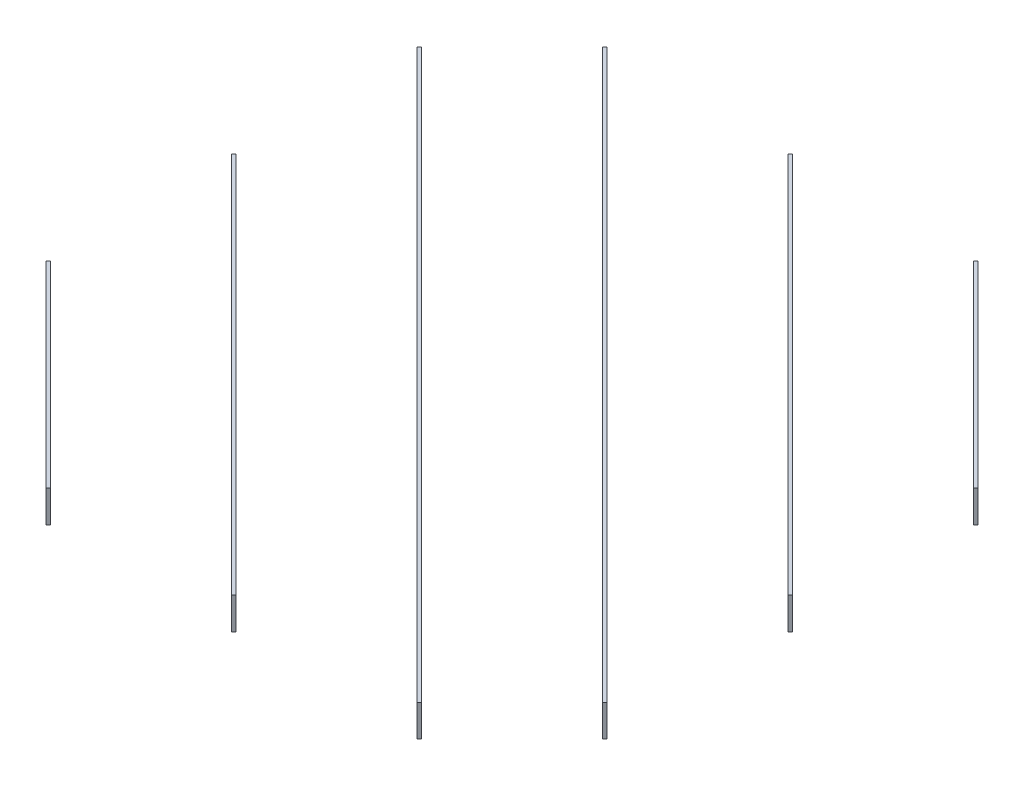
SolidWorks part; units mm, degrees
material "Plain Carbon Steel"
ref_plane "Front" through (0, 0, 0) normal (0, 0, 1) x (1, 0, 0)
ref_plane "Top" through (0, 0, 0) normal (0, 1, 0) x (1, 0, 0)
ref_plane "Right" through (0, 0, 0) normal (1, 0, 0) x (0, 0, -1)
sketch "Sketch1" plane through (0, 0, 0) normal (0, 1, 0) x (1, 0, 0)
  line L0 (-525, -525) -> (-525, 525) construction
  line L1 (-625, 625) -> (625, 625) construction
  line L2 (-625, 625) -> (-625, -625) construction
  line L3 (-625, -625) -> (625, -625) construction
  line L4 (625, 625) -> (625, -625) construction
  line L5 (-625, 625) -> (625, -625) construction
  line L6 (-625, -625) -> (625, 625) construction
  line L7 (-525, 525) -> (525, 525) construction
  line L8 (-525, 350) -> (525, 350) construction
  line L9 (-525, 175) -> (525, 175) construction
  line L10 (-525, 0) -> (525, 0) construction
  line L11 (-525, -175) -> (525, -175) construction
  line L12 (-525, -350) -> (525, -350) construction
  line L13 (-525, -525) -> (525, -525) construction
  line L14 (-350, -525) -> (-350, 525) construction
  line L15 (-175, -525) -> (-175, 525) construction
  line L16 (0, -525) -> (0, 525) construction
  line L17 (175, -525) -> (175, 525) construction
  line L18 (350, -525) -> (350, 525) construction
  line L19 (525, -525) -> (525, 525) construction
  line L20 (-620, 625) -> (620, 625) construction
  point P0 (0, 0)
  dimension "D5" = 175
  dimension "D3" = 7
  dimension "D4" = 7
sketch "Sketch2" plane through (0, 0, 0) normal (0, 1, 0) x (1, 0, 0)
  line L0 (-625, -254.2426) -> (-254.2426, -625)
  line L1 (-622.8787, 622.8787) -> (622.8787, 622.8787) construction
  line L2 (-622.8787, 622.8787) -> (-622.8787, -622.8787) construction
  line L3 (-622.8787, -622.8787) -> (622.8787, -622.8787) construction
  line L4 (622.8787, 622.8787) -> (622.8787, -622.8787) construction
  line L5 (-622.8787, 622.8787) -> (622.8787, -622.8787) construction
  line L6 (-622.8787, -622.8787) -> (622.8787, 622.8787) construction
  line L7 (-625, 625) -> (625, -625) construction
  line L8 (-447.8787, 622.8787) -> (622.8787, -447.8787) construction
  line L9 (-97.8787, 622.8787) -> (622.8787, -97.8787) construction
  line L10 (252.1213, 622.8787) -> (622.8787, 252.1213) construction
  line L11 (-622.8787, -252.1213) -> (-252.1213, -622.8787) construction
  line L12 (-622.8787, 97.8787) -> (97.8787, -622.8787) construction
  line L13 (-622.8787, 447.8787) -> (447.8787, -622.8787) construction
  line L14 (-625, 95.7574) -> (95.7574, -625)
  line L15 (-625, 445.7574) -> (445.7574, -625)
  line L16 (-450, 620.7574) -> (620.7574, -450)
  line L17 (-100, 620.7574) -> (620.7574, -100)
  line L18 (250, 620.7574) -> (620.7574, 250)
  line L19 (-620.7574, -250) -> (-250, -620.7574)
  line L20 (-620.7574, 100) -> (100, -620.7574)
  line L21 (-620.7574, 450) -> (450, -620.7574)
  line L22 (-445.7574, 625) -> (625, -445.7574)
  line L23 (-95.7574, 625) -> (625, -95.7574)
  line L24 (254.2426, 625) -> (625, 254.2426)
  line L25 (-625, -254.2426) -> (-620.7574, -250)
  line L26 (-254.2426, -625) -> (-250, -620.7574)
  line L27 (-625, 95.7574) -> (-620.7574, 100)
  line L28 (95.7574, -625) -> (100, -620.7574)
  line L29 (-625, 445.7574) -> (-620.7574, 450)
  line L30 (445.7574, -625) -> (450, -620.7574)
  line L31 (-450, 620.7574) -> (-445.7574, 625)
  line L32 (620.7574, -450) -> (625, -445.7574)
  line L33 (-100, 620.7574) -> (-95.7574, 625)
  line L34 (620.7574, -100) -> (625, -95.7574)
  line L35 (250, 620.7574) -> (254.2426, 625)
  line L36 (620.7574, 250) -> (625, 254.2426)
  line L38 (-625, 625) -> (625, 625) construction
  line L39 (625, 625) -> (625, -625) construction
extrude "Boss-Extrude1" add sketch "Sketch2" along normal blind 60
sketch "Sketch3" plane through (-439.6213, 0, 439.6213) normal (-0.7071, 0, 0.7071) x (0.7071, 0, 0.7071)
  line L0 (-742.4621, 0) -> (0, 0) construction
  line L1 (-126.7056, 30) -> (-120.7056, 30)
  line L2 (-126.7056, 30) -> (-126.7056, -30)
  line L3 (-126.7056, -30) -> (-120.7056, -30)
  line L4 (-120.7056, 30) -> (-120.7056, -30)
  line L5 (-126.7056, 30) -> (-120.7056, -30) construction
  line L6 (-126.7056, -30) -> (-120.7056, 30) construction
  line L7 (123.7437, 0) -> (-618.7184, 0) construction
  line L8 (-374.2311, 30) -> (-368.2311, 30)
  line L9 (-374.2311, 30) -> (-374.2311, -30)
  line L10 (-374.2311, -30) -> (-368.2311, -30)
  line L11 (-368.2311, 30) -> (-368.2311, -30)
  line L12 (-374.2311, 30) -> (-368.2311, -30) construction
  line L13 (-374.2311, -30) -> (-368.2311, 30) construction
  line L14 (-621.7184, 30) -> (-615.7184, 30)
  line L15 (-621.7184, 30) -> (-621.7184, -30)
  line L16 (-621.7184, -30) -> (-615.7184, -30)
  line L17 (-615.7184, 30) -> (-615.7184, -30)
  line L18 (-621.7184, 30) -> (-615.7184, -30) construction
  line L19 (-621.7184, -30) -> (-615.7184, 30) construction
  line L20 (0, 0) -> (0, 60) construction
  line L21 (-262.165, 60) -> (262.165, 60) construction
  line L22 (621.7184, -30) -> (615.7184, 30) construction
  line L23 (621.7184, 30) -> (615.7184, -30) construction
  line L24 (374.2311, -30) -> (368.2311, 30) construction
  line L25 (374.2311, 30) -> (368.2311, -30) construction
  line L26 (126.7056, -30) -> (120.7056, 30) construction
  line L27 (126.7056, 30) -> (120.7056, -30) construction
  line L28 (615.7184, 30) -> (615.7184, -30)
  line L29 (621.7184, -30) -> (615.7184, -30)
  line L30 (621.7184, 30) -> (621.7184, -30)
  line L31 (621.7184, 30) -> (615.7184, 30)
  line L32 (368.2311, 30) -> (368.2311, -30)
  line L33 (374.2311, -30) -> (368.2311, -30)
  line L34 (374.2311, 30) -> (374.2311, -30)
  line L35 (374.2311, 30) -> (368.2311, 30)
  line L36 (120.7056, 30) -> (120.7056, -30)
  line L37 (126.7056, -30) -> (120.7056, -30)
  line L38 (126.7056, 30) -> (126.7056, -30)
  line L39 (126.7056, 30) -> (120.7056, 30)
  circle A0 centre (-126.7056, 30) radius 1.5
  circle A1 centre (-120.7056, 30) radius 1.5
  circle A2 centre (-621.7184, 30) radius 1.5
  circle A3 centre (-615.7184, 30) radius 1.5
  circle A4 centre (-374.2311, 30) radius 1.5
  circle A5 centre (-368.2311, 30) radius 1.5
  circle A6 centre (368.2311, 30) radius 1.5
  circle A7 centre (374.2311, 30) radius 1.5
  circle A8 centre (615.7184, 30) radius 1.5
  circle A9 centre (621.7184, 30) radius 1.5
  circle A10 centre (120.7056, 30) radius 1.5
  circle A11 centre (126.7056, 30) radius 1.5
  point P0 (-123.7056, 0)
  point P7 (-371.2311, 0)
  point P12 (-618.7184, 0)
  point P48 (618.7184, 0)
  point P49 (371.2311, 0)
  point P50 (123.7056, 0)
  line M15 (-262.165, 0) -> (262.165, 0)
  dimension "D1" = 60
  dimension "D7" = 3
  dimension "D8" = 3
  dimension "D9" = 3
  dimension "D10" = 3
  dimension "D11" = 3
  dimension "D12" = 3
  dimension "D2" = 60
  dimension "D3" = 60
  dimension "D4" = 3
  dimension "D5" = 3
  dimension "D6" = 3
extrude "Cut-Extrude1" cut sketch "Sketch3" against normal through all contours A3 L14 A2 L15 L16 L17 | L14 A2 L15 | L17 A3 L14 | L14 A3 L17 | L15 A2 L14 | L8 A4 L9 | L9 A4 L8 | A5 L8 A4 L9 L10 L11 | L8 A5 L11 | L11 A5 L8 | L1 A0 L2 | L4 A1 L1 | L1 A1 L4 | A1 L1 A0 L2 L4 M15 | L2 A0 L1 | A10 L36 L39 | A10 L39 L36 | L38 A11 L39 A10 L36 M15 | A11 L38 L39 | A11 L39 L38 | A6 L32 L35 | L34 A7 L35 A6 L32 L33 | A7 L35 L34 | A7 L34 L35 | A6 L35 L32 | A8 L28 L31 | A9 L31 L30 | L30 A9 L31 A8 L28 L29 | A9 L30 L31 | A8 L31 L28
sketch "Sketch4" plane through (-439.6213, 0, 439.6213) normal (-0.7071, 0, 0.7071) x (0.7071, 0, 0.7071)
  line L0 (-120.7056, 0) -> (120.7056, 0) construction
  circle A0 centre (0, 0) radius 1.5
  dimension "D1" = 3
extrude "Cut-Extrude2" cut sketch "Sketch4" against normal through all
equation "\"Plate width\"= 60"
equation "\"D1@Boss-Extrude1\"=\"Plate width\""
equation "\"D1@Sketch3\"=\"Plate width\""
equation "\"D2@Sketch3\"=\"Plate width\""
equation "\"D3@Sketch3\"=\"Plate width\""
equation "\"D4@Sketch3\"=\"half plate thickness\""
equation "\"D5@Sketch3\"=\"half plate thickness\""
equation "\"D6@Sketch3\"=\"half plate thickness\""
equation "\"D7@Sketch3\"=\"half plate thickness\""
equation "\"D8@Sketch3\"=\"half plate thickness\""
equation "\"D9@Sketch3\"=\"half plate thickness\""
equation "\"D10@Sketch3\"=\"half plate thickness\""
equation "\"D11@Sketch3\"=\"half plate thickness\""
equation "\"D12@Sketch3\"=\"half plate thickness\""
